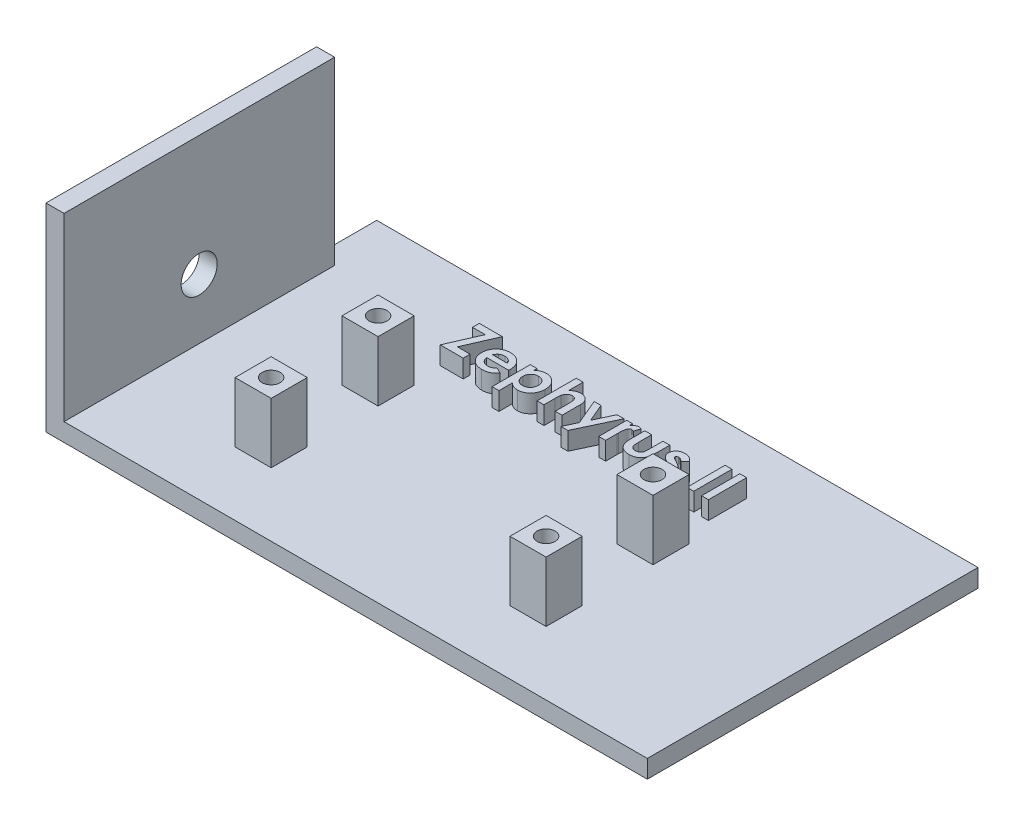
SolidWorks part; units mm, degrees
ref_plane "Front Plane" through (0, 0, 0) normal (0, 0, 1) x (1, 0, 0)
ref_plane "Top Plane" through (0, 0, 0) normal (0, 1, 0) x (1, 0, 0)
ref_plane "Right Plane" through (0, 0, 0) normal (1, 0, 0) x (0, 0, -1)
sketch "Sketch1" plane through (0, 0, 0) normal (0, 1, 0) x (1, 0, 0)
  line L0 (-77.6599, 55) -> (-77.6599, 0)
  line L1 (-77.6599, 0) -> (22.3401, 0)
  line L2 (22.3401, 0) -> (22.3401, 55)
  line L3 (22.3401, 55) -> (-77.6599, 55)
extrude "Boss-Extrude1" add sketch "Sketch1" along normal blind 3
sketch "Sketch2" plane through (0, 3, 0) normal (0, 1, 0) x (1, 0, 0)
  line L0 (-53.7962, 31.3632) -> (-53.7962, 13.5832) construction
  line L1 (-53.7962, 13.5832) -> (-8.0762, 13.5832) construction
  line L2 (-8.0762, 13.5832) -> (-8.0762, 31.3632) construction
  line L3 (-8.0762, 31.3632) -> (-53.7962, 31.3632) construction
  line L5 (-56.7962, 34.3632) -> (-50.7962, 34.3632)
  line L6 (-56.7962, 34.3632) -> (-56.7962, 28.3632)
  line L7 (-56.7962, 28.3632) -> (-50.7962, 28.3632)
  line L8 (-50.7962, 34.3632) -> (-50.7962, 28.3632)
  line L9 (-56.7962, 34.3632) -> (-50.7962, 28.3632) construction
  line L10 (-56.7962, 28.3632) -> (-50.7962, 34.3632) construction
  line L11 (-11.0762, 34.3632) -> (-5.0762, 34.3632)
  line L12 (-11.0762, 34.3632) -> (-11.0762, 28.3632)
  line L13 (-11.0762, 28.3632) -> (-5.0762, 28.3632)
  line L14 (-5.0762, 34.3632) -> (-5.0762, 28.3632)
  line L15 (-11.0762, 34.3632) -> (-5.0762, 28.3632) construction
  line L16 (-11.0762, 28.3632) -> (-5.0762, 34.3632) construction
  line L17 (-11.0762, 16.5832) -> (-5.0762, 16.5832)
  line L18 (-11.0762, 16.5832) -> (-11.0762, 10.5832)
  line L19 (-11.0762, 10.5832) -> (-5.0762, 10.5832)
  line L20 (-5.0762, 16.5832) -> (-5.0762, 10.5832)
  line L21 (-11.0762, 16.5832) -> (-5.0762, 10.5832) construction
  line L22 (-11.0762, 10.5832) -> (-5.0762, 16.5832) construction
  line L23 (-56.7962, 16.5832) -> (-50.7962, 16.5832)
  line L24 (-56.7962, 16.5832) -> (-56.7962, 10.5832)
  line L25 (-56.7962, 10.5832) -> (-50.7962, 10.5832)
  line L26 (-50.7962, 16.5832) -> (-50.7962, 10.5832)
  line L27 (-56.7962, 16.5832) -> (-50.7962, 10.5832) construction
  line L28 (-56.7962, 10.5832) -> (-50.7962, 16.5832) construction
extrude "Boss-Extrude2" add sketch "Sketch2" along normal blind 10
sketch "Sketch3" plane through (0, 13, 0) normal (0, 1, 0) x (1, 0, 0)
  line L0 (-53.7962, 31.3632) -> (-53.7962, 13.5832) construction
  line L3 (-53.7962, 13.5832) -> (-8.0762, 13.5832) construction
  line L6 (-53.7962, 31.3632) -> (-8.0762, 31.3632) construction
  line L9 (-8.0762, 31.3632) -> (-8.0762, 13.5832) construction
  circle A0 centre (-53.7962, 31.3632) radius 1.5
  circle A1 centre (-8.0762, 31.3632) radius 1.5
  circle A2 centre (-8.0762, 13.5832) radius 1.5
  circle A3 centre (-53.7962, 13.5832) radius 1.5
extrude "Cut-Extrude1" cut sketch "Sketch3" against normal through all and the other way through all
sketch "Sketch4" plane through (0, 3, 0) normal (0, 1, 0) x (1, 0, 0)
  line L2 (-74.6599, 45) -> (-74.6599, 0)
  line L3 (-77.6599, 0) -> (22.3401, 0) construction
  line L4 (-74.6599, 0) -> (-77.6599, 0)
  line L6 (-77.6599, 0) -> (-77.6599, 45)
  line L7 (-77.6599, 45) -> (-74.6599, 45)
extrude "Boss-Extrude3" add sketch "Sketch4" along normal blind 30
sketch "Sketch5" plane through (-74.6599, 0, 0) normal (1, 0, 0) x (0, 0, -1)
  line L0 (10.5832, 13) -> (34.3632, 13) construction
  circle A0 centre (22.4732, 13) radius 3
extrude "Cut-Extrude2" cut sketch "Sketch5" against normal blind 30
sketch "Sketch6" plane through (0, 0, 0) normal (0, -1, 0) x (1, 0, 0)
  circle A0 centre (-53.7962, -13.5832) radius 3
  circle A1 centre (-8.0762, -13.5832) radius 3
  circle A2 centre (-8.0762, -31.3632) radius 3
  circle A3 centre (-53.7962, -31.3632) radius 3
extrude "Cut-Extrude3" cut sketch "Sketch6" against normal blind 1.5
sketch "Sketch7" plane through (-77.6599, 0, 0) normal (-1, 0, 0) x (0, 0, 1)
  line L0 (-41.1408, 21.0108) -> (-2.7445, 21.0108) construction
  text T0 "<b>Zephyrus II</b>" font "Century Gothic" height in points 18
  point P3 (-2.7445, 21.0108)
  point P4 (-41.1408, 21.0108)
extrude "Boss-Extrude4" add sketch "Sketch7" along normal blind 2
sketch "Sketch8" plane through (0, 3, 0) normal (0, 1, 0) x (1, 0, 0)
  line L0 (-59.1775, 39.3456) -> (0, 39.3456) construction
  text T0 "<b>Zephyrus II</b>" font "Century Gothic" height in points 24
extrude "Boss-Extrude5" add sketch "Sketch8" along normal blind 3
